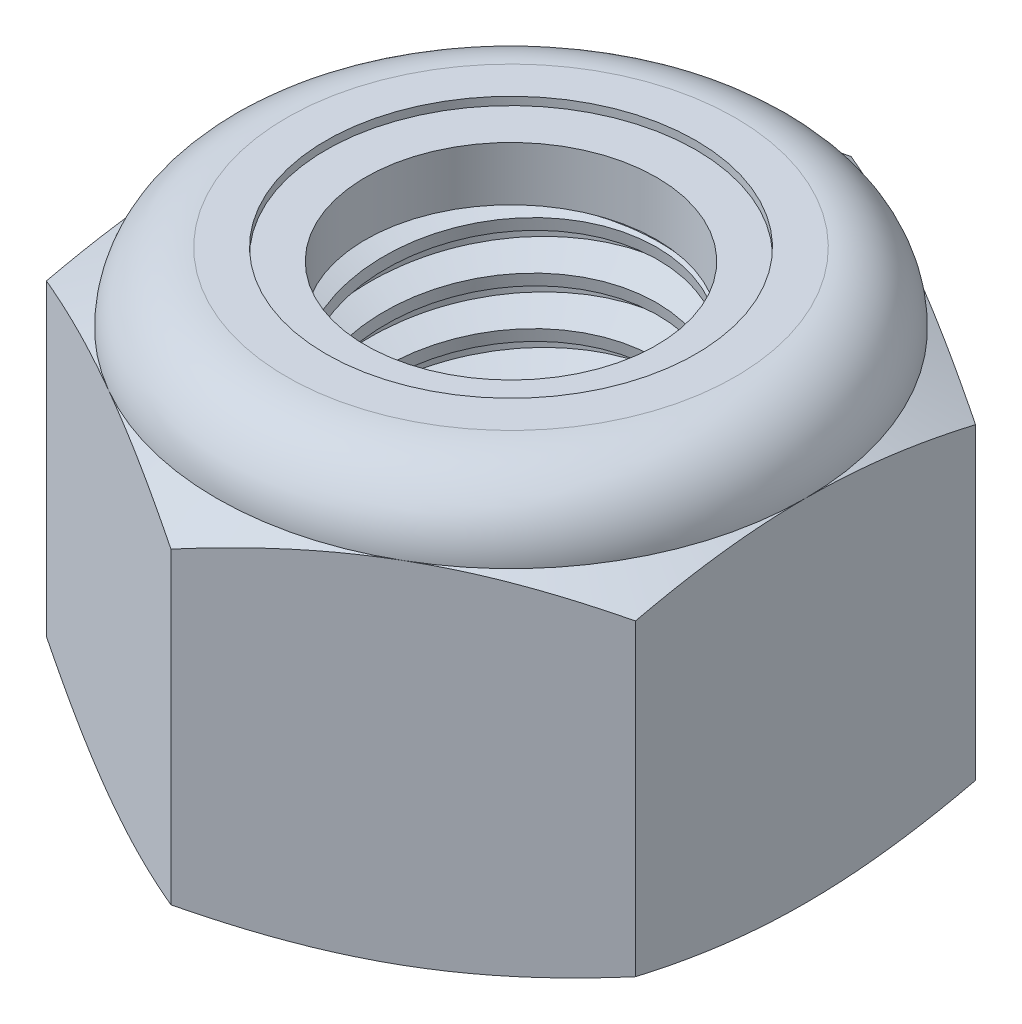
SolidWorks part; units mm, degrees
ref_plane "Front" through (0, 0, 0) normal (0, 0, 1) x (1, 0, 0)
ref_plane "Top" through (0, 0, 0) normal (0, 1, 0) x (1, 0, 0)
ref_plane "Right" through (0, 0, 0) normal (1, 0, 0) x (0, 0, -1)
sketch "Sketch1" plane through (0, 0, 0) normal (0, 1, 0) x (1, 0, 0)
  line L1 (0, 6.4158) -> (-5.5563, 3.2079)
  line L2 (-5.5563, 3.2079) -> (-5.5563, -3.2079)
  line L3 (-5.5563, -3.2079) -> (0, -6.4158)
  line L4 (0, -6.4158) -> (5.5562, -3.2079)
  line L5 (5.5562, -3.2079) -> (5.5562, 3.2079)
  line L6 (5.5562, 3.2079) -> (0, 6.4158)
  circle A0 centre (0, 0) radius 5.5563 construction
  dimension "Hex Flats" = 11.1125
extrude "Extrude1" add sketch "Sketch1" along normal blind 7.9375
sketch "Sketch2" plane through (0, 0, 0) normal (1, 0, 0) x (0, 0, -1)
  line L0 (-3.175, 0) -> (-3.175, 7.9375) construction
  line L1 (0, 0) -> (3.175, 0)
  line L2 (0, 0) -> (0, 7.9375)
  line L3 (0, 7.9375) -> (3.175, 7.9375)
  line L4 (3.175, 0) -> (3.175, 7.9375)
  line L5 (-3.2079, 7.9375) -> (3.2079, 7.9375) construction
  line L7 (0, -3.175) -> (0, 0) construction
  dimension "Thread Dia" = 6.35
revolve "Revolve1" add sketch "Sketch2" angle 360 about L7
sketch "Sketch3" plane through (0, 0, 0) normal (1, 0, 0) x (0, 0, -1)
  line L0 (3.175, 7.9375) -> (-3.175, 7.9375) construction
  line L1 (-3.175, 7.9375) -> (-3.175, 7.0304) construction
  line L2 (-3.175, 7.0304) -> (3.175, 7.9375) construction
  line L3 (3.175, 7.9375) -> (3.191, 7.8252) construction
  line L4 (3.191, 7.8252) -> (3.3033, 7.0395)
  line L5 (3.3033, 7.0395) -> (2.7771, 7.2507)
  line L6 (2.7771, 7.2507) -> (2.7451, 7.4752)
  line L7 (2.7451, 7.4752) -> (3.191, 7.8252)
  line L8 (2.7611, 7.3629) -> (3.2472, 7.4324) construction
  line L9 (3.175, 7.9375) -> (3.175, 7.4221) construction
  line L10 (3.175, 7.4221) -> (-3.175, 6.5149) construction
  line L11 (-3.175, 6.5149) -> (-3.175, 7.0304) construction
  line L12 (-0.1384, 7.9375) -> (0.1384, 5.9995) construction
  line L13 (-3.175, 0) -> (-3.175, 7.9375) construction
  line L14 (0, 7.9375) -> (3.175, 7.9375) construction
  line L15 (3.175, 0) -> (3.175, 7.9375) construction
  point P13 (0, 6.9685)
  dimension "D1" = 0.1134
  dimension "D2" = 0.2268
  dimension "Thread Pitch" = 0.9071
  dimension "D4" = 60
  dimension "D5" = 0.9071
revolve "Cut-Revolve1" cut sketch "Sketch3" angle 360 about L12
pattern_linear "LPattern1" count 9 spacing 0.9071 along (0, -1, 0) count 2 spacing 0.9071 along (0, 1, 0) of "Cut-Revolve1"
sketch "Sketch4" plane through (0, 0, 0) normal (1, 0, 0) x (0, 0, -1)
  line L0 (0, 7.9375) -> (3.175, 7.9375)
  line L1 (3.175, 7.9375) -> (2.7451, 7.737)
  line L2 (2.7451, 7.737) -> (2.7451, 0.2005)
  line L3 (2.7451, 0.2005) -> (3.175, 0)
  line L4 (3.175, 0) -> (0, 0)
  line L5 (0, 0) -> (0, 7.9375)
  line L6 (3.175, 0) -> (3.175, 7.9375) construction
  line L7 (0, 7.9375) -> (3.175, 7.9375) construction
  line L8 (0, 0) -> (3.175, 0) construction
  line L9 (0, 0) -> (0, 7.9375) construction
  line L10 (0, 7.9375) -> (0, 8.4119) construction
  dimension "D1" = 25
revolve "Cut-Revolve2" cut sketch "Sketch4" angle 360 about L10
combine bodies "Combine1" operation type subtract main body 112 bodies to subtract 111
sketch "Sketch5" plane through (0, 0, 0) normal (1, 0, 0) x (0, 0, -1)
  line L0 (0, 0) -> (5.5563, 0)
  line L1 (5.5563, 0) -> (6.4158, 0.4008)
  line L2 (6.4158, 0.4008) -> (6.4158, 6.2138)
  line L3 (6.4158, 6.2138) -> (5.5563, 6.6146)
  line L4 (4.2333, 7.9375) -> (4.2333, 9.2075)
  line L5 (4.2333, 9.2075) -> (7.6858, 9.2075)
  line L6 (7.6858, 9.2075) -> (7.6858, -1.27)
  line L7 (7.6858, -1.27) -> (0, -1.27)
  line L8 (0, -1.27) -> (0, 0)
  line L9 (5.5563, 6.6146) -> (5.5563, 0) construction
  line L10 (0, 0) -> (3.175, 0) construction
  line L13 (6.4158, 3.3073) -> (7.6858, 3.3073) construction
  line L14 (6.4158, 7.9375) -> (6.4158, 0) construction
  line L15 (0, 0) -> (0, 9.2075) construction
  line L20 (0, 9.2075) -> (4.2333, 9.2075) construction
  line L22 (0, 7.9375) -> (3.175, 7.9375) construction
  arc A0 (5.5563, 6.6146) -> (4.2333, 7.9375) centre (4.2333, 6.6146) ccw
  dimension "D1" = 25
  dimension "D2" = 1.27
  dimension "D3" = 7.9375
  dimension "D4" = 1.3229
revolve "Cut-Revolve3" cut sketch "Sketch5" angle 360 about L15
sketch "Sketch6" plane through (0, 0, 0) normal (1, 0, 0) x (0, 0, -1)
  line L0 (0, 6.6146) -> (5.4039, 6.6146)
  line L1 (4.2333, 7.7851) -> (3.4892, 7.7851)
  line L2 (0, 9.2075) -> (0, 6.6146)
  line L3 (3.4892, 9.2075) -> (0, 9.2075)
  line L4 (0, 9.2075) -> (4.2333, 9.2075) construction
  line L5 (0, 0) -> (0, 9.2075) construction
  line L6 (0, 9.2075) -> (0, 44.323) construction
  line L7 (3.4892, 7.7851) -> (3.4892, 9.2075)
  line L8 (4.2333, 7.9375) -> (4.2333, 7.7851) construction
  line L9 (3.4892, 7.7851) -> (2.7451, 7.7851) construction
  line L10 (2.7451, 7.7851) -> (2.7451, 7.737) construction
  arc A0 (5.4039, 6.6146) -> (4.2333, 7.7851) centre (4.2333, 6.6146) ccw
  arc A1 (5.5563, 6.6146) -> (4.2333, 7.9375) centre (4.2333, 6.6146) ccw construction
  dimension "D1" = 0.1524
revolve "Cut-Revolve4" cut sketch "Sketch6" angle 360 about L6
sketch "Sketch7" plane through (0, 0, 0) normal (1, 0, 0) x (0, 0, -1)
  line L0 (2.7451, 6.6908) -> (5.325, 6.6908)
  line L1 (4.2333, 7.7089) -> (2.7451, 7.7089)
  line L2 (2.7451, 7.7089) -> (2.7451, 6.6908)
  line L3 (2.7451, 6.6908) -> (0, 6.6908) construction
  line L4 (0, 6.6908) -> (0, 7.7089) construction
  line L5 (0, 7.7089) -> (2.7451, 7.7089) construction
  line L6 (2.7451, 6.6908) -> (2.7451, 6.6146) construction
  line L7 (0, 6.6146) -> (5.4039, 6.6146) construction
  line L8 (4.2333, 7.7089) -> (4.2333, 7.7851) construction
  arc A0 (5.325, 6.6908) -> (4.2333, 7.7089) centre (4.2333, 6.6146) ccw
  arc A2 (5.4039, 6.6146) -> (4.2333, 7.7851) centre (4.2333, 6.6146) ccw construction
  dimension "D1" = 0.0762
revolve "Revolve2" add sketch "Sketch7" angle 360 about L4
equation "\"D1@Sketch3\"=\"Thread Pitch@Sketch3\"/8"
equation "\"D2@Sketch3\"=\"Thread Pitch@Sketch3\"/4"
equation "\"D5@Sketch3\"=\"Thread Pitch@Sketch3\""
equation "\"D4@LPattern1\"=\"Thread Pitch@Sketch3\""
equation "\"D3@LPattern1\"=\"Thread Pitch@Sketch3\""
equation "\"D1@LPattern1\"=\"Height@Extrude1\"/\"Thread Pitch@Sketch3\""
equation "\"D4@Sketch5\"=\"Height@Extrude1\"/6"
